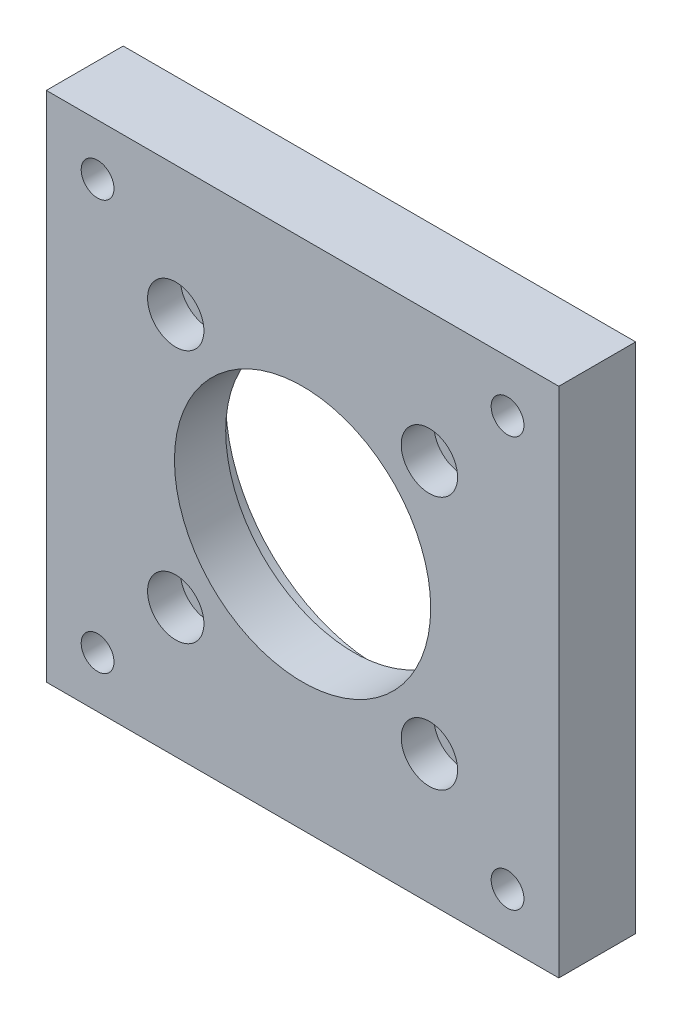
SolidWorks part; units mm, degrees
ref_plane "前视基准面" through (0, 0, 0) normal (0, 0, 1) x (1, 0, 0)
ref_plane "上视基准面" through (0, 0, 0) normal (0, 1, 0) x (1, 0, 0)
ref_plane "右视基准面" through (0, 0, 0) normal (1, 0, 0) x (0, 0, -1)
sketch "草图1" plane through (0, 0, 0) normal (0, 0, 1) x (1, 0, 0)
  line L1 (50, -50) -> (-50, -50)
  line L2 (50, -50) -> (50, 50)
  line L3 (50, 50) -> (-50, 50)
  line L4 (-50, -50) -> (-50, 50)
  line L5 (50, -50) -> (-50, 50) construction
  line L6 (50, 50) -> (-50, -50) construction
  point P0 (0, 0)
  dimension "D1" = 100
  dimension "D2" = 100
extrude "凸台-拉伸1" add sketch "草图1" along normal blind 15
sketch "草图2" plane through (0, 0, 0) normal (0, 0, 1) x (1, 0, 0)
  line L1 (40, -40) -> (-40, -40)
  line L2 (40, -40) -> (40, 40)
  line L3 (40, 40) -> (-40, 40)
  line L4 (-40, -40) -> (-40, 40)
  line L5 (40, -40) -> (-40, 40) construction
  line L6 (40, 40) -> (-40, -40) construction
  point P0 (0, 0)
  dimension "D1" = 80
hole_wizard "M6 六角凹头螺钉的柱形沉头孔1" positions "3D草图1" profile "草图3" counterbore size "M6" standard "Iso" end condition through all
sketch3d "3D草图1"
  point P0 (-40, 40, 0)
  point P3 (40, 40, 0)
  point P6 (40, -40, 0)
  point P9 (-40, -40, 0)
sketch "草图3" plane through (-40, 40, 0) normal (1, 0, 0) x (0, 1, 0)
  line L0 (0, 0) -> (0, 15)
  line L1 (0, 15) -> (3.2, 15)
  line L3 (3.2, 15) -> (3.2, 6.4)
  line L4 (3.2, 6.4) -> (5.5, 6.4)
  line L5 (5.5, 6.4) -> (5.5, 0)
  line L7 (5.5, 0) -> (0, 0)
  line L11 (0, -6.35) -> (0, 107.95) construction
  dimension "通孔孔直径" = 6.4
  dimension "通孔孔深度" = 15
  dimension "柱形沉头孔直径" = 11
  dimension "柱形沉头孔深度" = 6.4
sketch "草图4" plane through (0, 0, 0) normal (0, 0, 1) x (1, 0, 0)
  circle A0 centre (0, 0) radius 30
  dimension "D1" = 60
extrude "切除-拉伸1" cut sketch "草图4" along normal blind 5
sketch "草图5" plane through (0, 0, 15) normal (0, 0, -1) x (-1, 0, 0)
  line L1 (24.7487, -24.7487) -> (-24.7487, -24.7487)
  line L2 (24.7487, -24.7487) -> (24.7487, 24.7487)
  line L3 (24.7487, 24.7487) -> (-24.7487, 24.7487)
  line L4 (-24.7487, -24.7487) -> (-24.7487, 24.7487)
  line L5 (24.7487, -24.7487) -> (-24.7487, 24.7487) construction
  line L6 (24.7487, 24.7487) -> (-24.7487, -24.7487) construction
  circle A0 centre (0, 0) radius 35
  dimension "D1" = 70
hole_wizard "M6 六角凹头螺钉的柱形沉头孔2" positions "3D草图3" profile "草图7" counterbore size "M6" standard "Iso" end condition through all
sketch3d "3D草图3"
  point P5 (-24.7487, 24.7487, 15)
  point P8 (-24.7487, -24.7487, 15)
  point P11 (24.7487, -24.7487, 15)
  point P14 (24.7487, 24.7487, 15)
sketch "草图7" plane through (-24.7487, 24.7487, 15) normal (1, 0, 0) x (0, -1, 0)
  line L0 (0, 0) -> (0, 15)
  line L1 (0, 15) -> (3.2, 15)
  line L3 (3.2, 15) -> (3.2, 6.4)
  line L4 (3.2, 6.4) -> (5.5, 6.4)
  line L5 (5.5, 6.4) -> (5.5, 0)
  line L7 (5.5, 0) -> (0, 0)
  line L11 (0, -6.35) -> (0, 107.95) construction
  dimension "通孔孔直径" = 6.4
  dimension "通孔孔深度" = 15
  dimension "柱形沉头孔直径" = 11
  dimension "柱形沉头孔深度" = 6.4
sketch "草图8" plane through (0, 0, 5) normal (0, 0, -1) x (-1, 0, 0)
  circle A0 centre (0, 0) radius 25
  dimension "D1" = 50
extrude "切除-拉伸2" cut sketch "草图8" against normal through all
